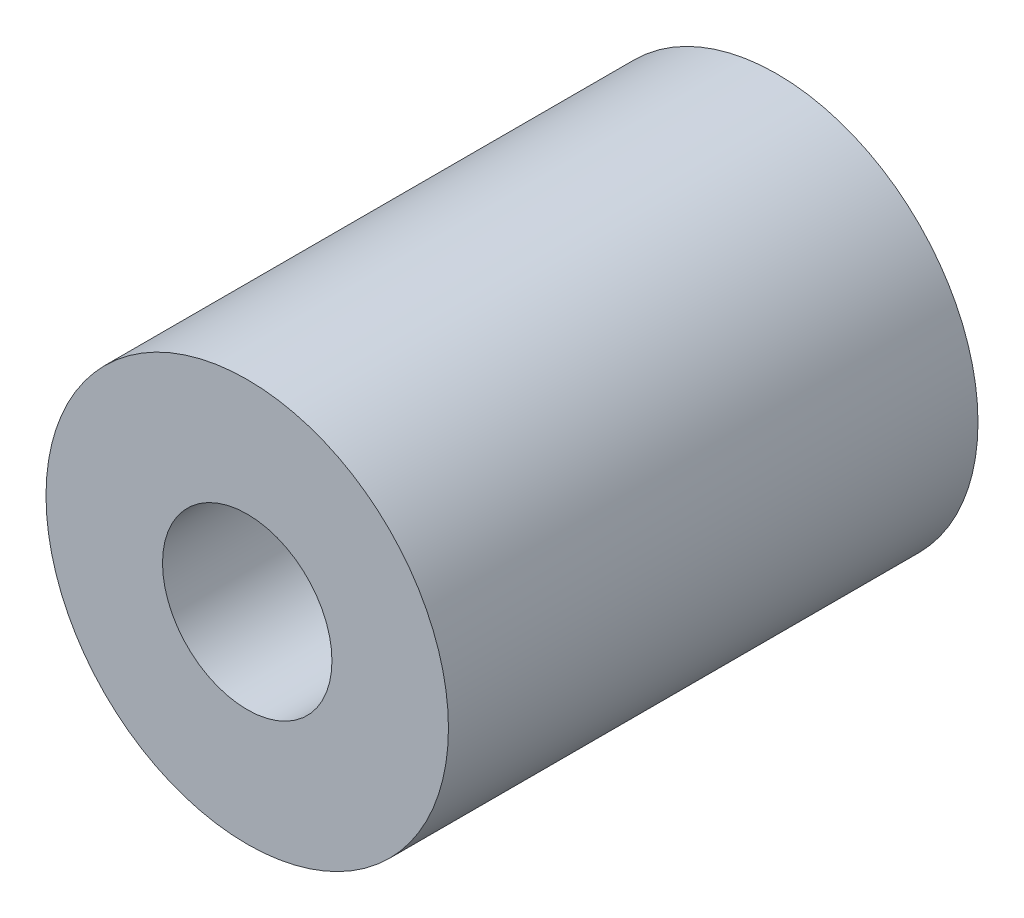
SolidWorks part; units mm, degrees
ref_plane "Front Plane" through (0, 0, 0) normal (0, 0, 1) x (1, 0, 0)
ref_plane "Top Plane" through (0, 0, 0) normal (0, 1, 0) x (1, 0, 0)
ref_plane "Right Plane" through (0, 0, 0) normal (1, 0, 0) x (0, 0, -1)
sketch "Sketch1" plane through (0, 0, 0) normal (0, 0, 1) x (1, 0, 0)
  circle A0 centre (0, 0) radius 4
  circle A1 centre (0, 0) radius 9.5
  dimension "D1" = 8
  dimension "D2" = 19
extrude "Boss-Extrude1" add sketch "Sketch1" along normal blind 25
